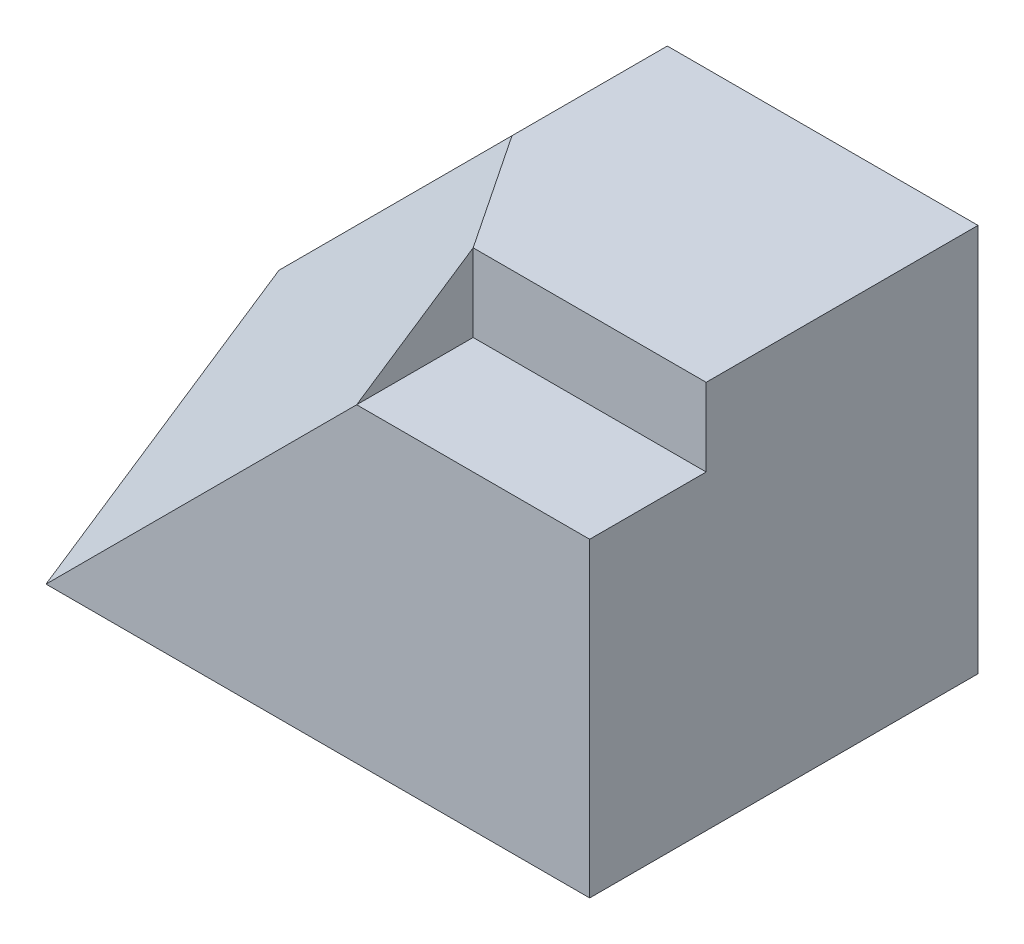
SolidWorks part; units mm, degrees
ref_plane "Front Plane" through (0, 0, 0) normal (0, 0, 1) x (1, 0, 0)
ref_plane "Top Plane" through (0, 0, 0) normal (0, 1, 0) x (1, 0, 0)
ref_plane "Right Plane" through (0, 0, 0) normal (1, 0, 0) x (0, 0, -1)
sketch "Sketch1" plane through (0, 0, 0) normal (0, 0, 1) x (1, 0, 0)
  line L1 (0, 0) -> (70, 0)
  line L2 (0, 0) -> (0, 50)
  line L3 (0, 50) -> (70, 50)
  line L4 (70, 0) -> (70, 50)
  dimension "D1" = 70
  dimension "D2" = 50
extrude "Boss-Extrude1" add sketch "Sketch1" along normal blind 50
sketch "Sketch2" plane through (0, 0, 50) normal (0, 0, 1) x (1, 0, 0)
  line L0 (0, 20) -> (30, 50)
  line L1 (0, 50) -> (0, 0) construction
  line L2 (70, 50) -> (0, 50) construction
  line L3 (30, 50) -> (0, 50)
  line L4 (0, 50) -> (0, 20)
  dimension "D1" = 30
  dimension "D2" = 30
extrude "Cut-Extrude1" cut sketch "Sketch2" against normal blind 50
sketch "Sketch3" plane through (0, 0, 50) normal (0, 0, 1) x (1, 0, 0)
  line L0 (0, 0) -> (40, 40)
  line L1 (40, 40) -> (40, 50)
  line L2 (70, 50) -> (30, 50) construction
  line L3 (40, 50) -> (30, 50)
  line L4 (30, 50) -> (0, 20)
  line L5 (0, 20) -> (0, 0)
  dimension "D1" = 10
extrude "Cut-Extrude3" cut sketch "Sketch3" against normal blind 30
ref_plane "Plane1" through (-13.6364, 13.6364, 9.0909) normal (-0.6396, 0.6396, 0.4264) x (0.7687, 0.5322, 0.3548)
sketch "Sketch4" plane through (-13.6364, 13.6364, 9.0909) normal (-0.6396, 0.6396, 0.4264) x (0.7687, 0.5322, 0.3548)
  line L0 (17.7394, -5.547) -> (17.7394, -41.6025)
  line L1 (17.7394, -41.6025) -> (69.7749, -19.4145)
  line L2 (69.7749, -19.4145) -> (56.766, 11.094)
  line L3 (56.766, 11.094) -> (17.7394, -5.547)
extrude "Boss-Extrude2" add sketch "Sketch4" against normal blind 30
sketch "Sketch6" plane through (0, 0, 0) normal (0, -1, 0) x (1, 0, 0)
  line L1 (0, 50) -> (70, 50)
  line L2 (0, 50) -> (0, 0)
  line L3 (0, 0) -> (70, 0)
  line L4 (70, 50) -> (70, 0)
extrude "Cut-Extrude4" cut sketch "Sketch6" along normal blind 30
sketch "Sketch7" plane through (0, 0, 0) normal (-1, 0, 0) x (0, 0, 1)
  line L0 (20, 20) -> (20, 0)
  line L1 (20, 0) -> (50, 0)
  line L2 (50, 0) -> (20, 20)
extrude "Boss-Extrude3" add sketch "Sketch7" against normal blind 30
sketch "Sketch8" plane through (0, 0, 50) normal (0, 0, 1) x (1, 0, 0)
  line L1 (40, 40) -> (70, 40)
  line L2 (40, 40) -> (40, 50)
  line L3 (40, 50) -> (70, 50)
  line L4 (70, 40) -> (70, 50)
extrude "Cut-Extrude6" cut sketch "Sketch8" against normal blind 15
ref_plane "Plane2" through (-13.6364, 13.6364, 9.0909) normal (0.6396, -0.6396, -0.4264) x (-0.7687, -0.5322, -0.3548)
sketch "Sketch9" plane through (-13.6364, 13.6364, 9.0909) normal (0.6396, -0.6396, -0.4264) x (-0.7687, -0.5322, -0.3548)
  line L0 (-56.766, 11.094) -> (-69.7749, -19.4145)
  line L1 (-69.7749, -19.4145) -> (-69.7749, -1.3868)
  line L2 (-69.7749, -1.3868) -> (-56.766, 11.094)
extrude "Boss-Extrude4" add sketch "Sketch9" along normal blind 15
sketch "Sketch10" plane through (0, 50, 0) normal (0, 1, 0) x (1, 0, 0)
  line L0 (30, -20) -> (40, -20)
  line L1 (40, -20) -> (40, -35)
  line L2 (40, -35) -> (30, -20)
extrude "Boss-Extrude5" add sketch "Sketch10" against normal blind 15
sketch "Sketch11" plane through (70, 0, 0) normal (1, 0, 0) x (0, 0, -1)
  line L1 (-50, 40) -> (-35, 40)
  line L2 (-50, 40) -> (-50, 50)
  line L3 (-50, 50) -> (-35, 50)
  line L4 (-35, 40) -> (-35, 50)
extrude "Cut-Extrude8" cut sketch "Sketch11" against normal blind 30
